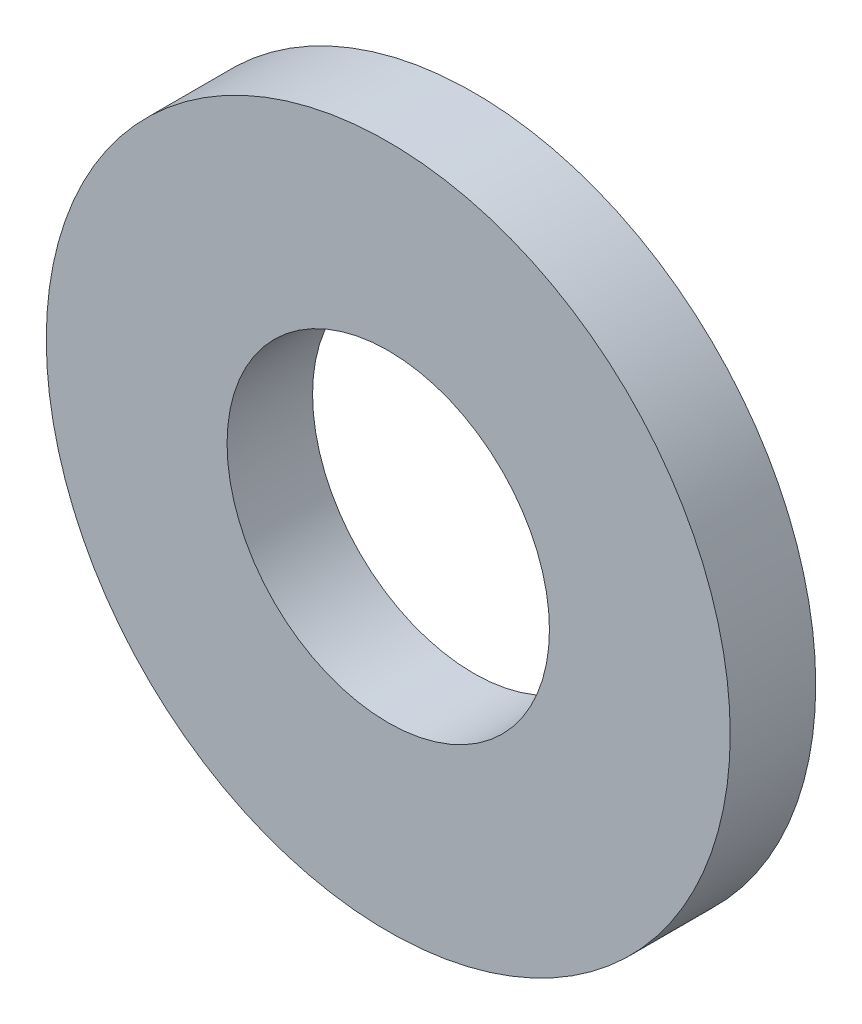
SolidWorks part; units mm, degrees
ref_plane "Front Plane" through (0, 0, 0) normal (0, 0, 1) x (1, 0, 0)
ref_plane "Top Plane" through (0, 0, 0) normal (0, 1, 0) x (1, 0, 0)
ref_plane "Right Plane" through (0, 0, 0) normal (1, 0, 0) x (0, 0, -1)
sketch "Sketch1" plane through (0, 0, 0) normal (0, 0, 1) x (1, 0, 0)
  circle A0 centre (0, 0) radius 2.993
  circle A1 centre (0, 0) radius 6.35
  dimension "D1" = 5.986
  dimension "D2" = 12.7
extrude "Boss-Extrude1" add sketch "Sketch1" along normal blind 1.5875
